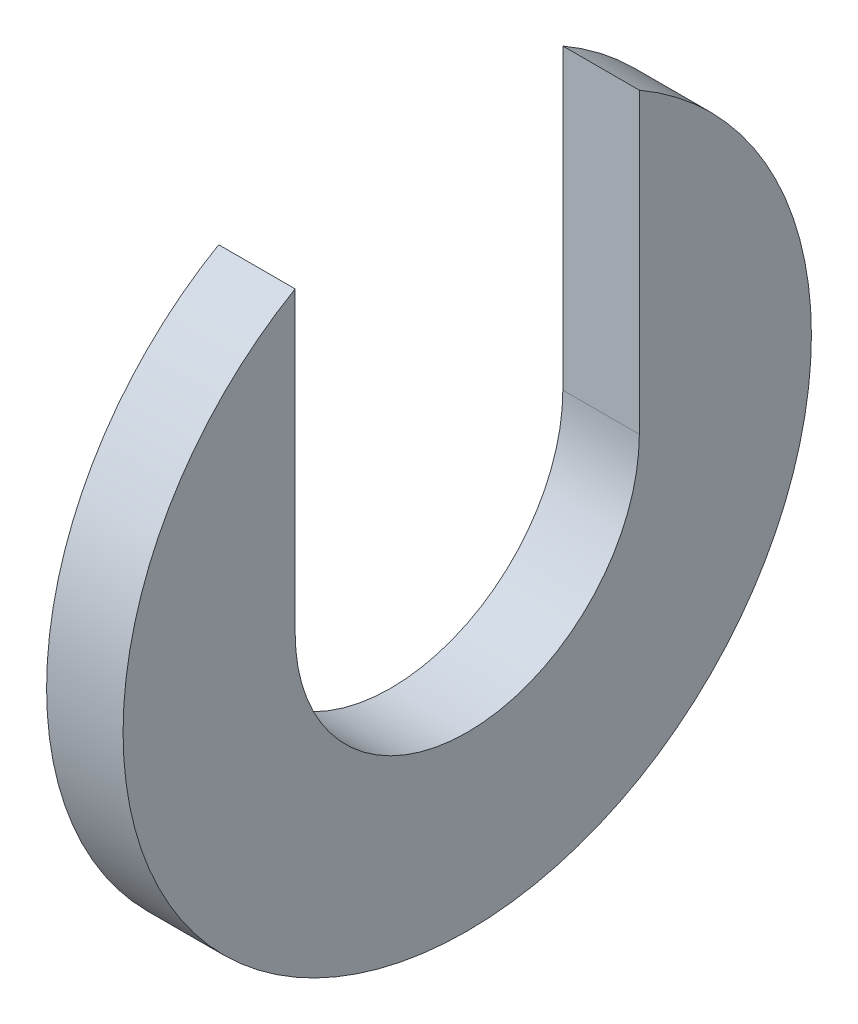
SolidWorks part; units mm, degrees
material "Cast Alloy Steel"
ref_plane "Front Plane" through (0, 0, 0) normal (0, 0, 1) x (1, 0, 0)
ref_plane "Top Plane" through (0, 0, 0) normal (0, 1, 0) x (1, 0, 0)
ref_plane "Right Plane" through (0, 0, 0) normal (1, 0, 0) x (0, 0, -1)
sketch "Sketch1" plane through (0, 0, 0) normal (1, 0, 0) x (0, 0, -1)
  line L0 (0, 4.5) -> (0, 9)
  circle A0 centre (0, 0) radius 9
  circle A1 centre (0, 0) radius 4.5
  dimension "D1" = 9
  dimension "D2" = 18
extrude "Boss-Extrude1" add sketch "Sketch1" along normal mid plane 2
sketch "Sketch3" plane through (0, 0, 0) normal (0, 1, 0) x (1, 0, 0)
  line L0 (-1, 0) -> (1, 0)
  line L1 (-1, 9) -> (-1, -9) construction
  line L2 (1, -9) -> (1, 9) construction
extrude "Cut-Extrude-Thin1" cut sketch "Sketch3" along normal through all thin thin type mid plane wall 9
